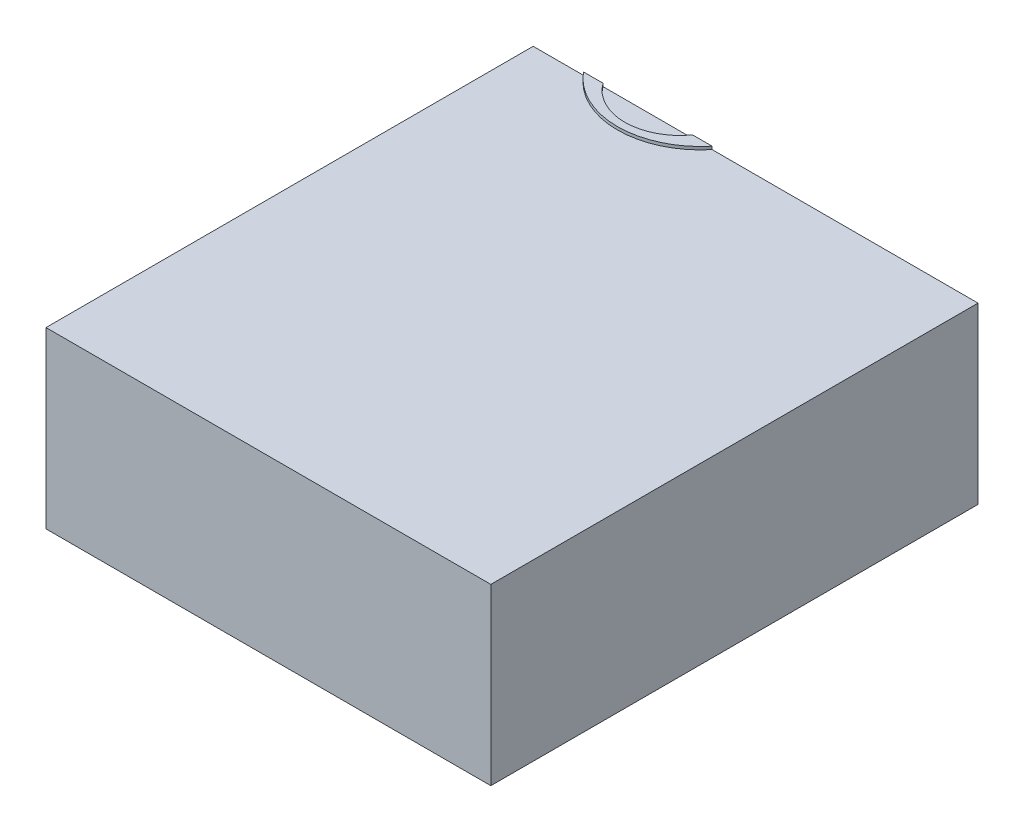
SolidWorks part; units mm, degrees
ref_plane "Front Plane" through (0, 0, 0) normal (0, 0, 1) x (1, 0, 0)
ref_plane "Top Plane" through (0, 0, 0) normal (0, 1, 0) x (1, 0, 0)
ref_plane "Right Plane" through (0, 0, 0) normal (1, 0, 0) x (0, 0, -1)
sketch "Sketch1" plane through (0, 0, 0) normal (0, 1, 0) x (1, 0, 0)
  circle A0 centre (0, 0) radius 28.1
extrude "Boss-Extrude1" add sketch "Sketch1" along normal blind 1
sketch "Sketch2" plane through (0, 1, 0) normal (0, 1, 0) x (1, 0, 0)
  circle A0 centre (0, -7) radius 18.6
extrude "Cut-Extrude1" cut sketch "Sketch2" against normal blind 58.8
sketch "Sketch3" plane through (0, 0, 0) normal (0, -1, 0) x (-1, 0, 0)
  line L1 (111.3415, -182.1414) -> (-111.3415, -182.1414)
  line L2 (111.3415, -182.1414) -> (111.3415, 182.1414)
  line L3 (111.3415, 182.1414) -> (-111.3415, 182.1414)
  line L4 (-111.3415, -182.1414) -> (-111.3415, 182.1414)
  line L5 (111.3415, -182.1414) -> (-111.3415, 182.1414) construction
  line L6 (111.3415, 182.1414) -> (-111.3415, -182.1414) construction
  point P0 (0, 0)
extrude "Boss-Extrude2" add sketch "Sketch3" along normal blind 58.8
sketch "Sketch4" plane through (0, -58.8, 0) normal (0, -1, 0) x (-1, 0, 0)
  line L1 (103.9587, -174.2721) -> (-103.9587, -174.2721)
  line L2 (103.9587, -174.2721) -> (103.9587, 174.2721)
  line L3 (103.9587, 174.2721) -> (-103.9587, 174.2721)
  line L4 (-103.9587, -174.2721) -> (-103.9587, 174.2721)
  line L5 (103.9587, -174.2721) -> (-103.9587, 174.2721) construction
  line L6 (103.9587, 174.2721) -> (-103.9587, -174.2721) construction
  point P0 (0, 0)
extrude "Cut-Extrude2" cut sketch "Sketch4" against normal blind 55.8
sketch "Sketch6" plane through (0, 1, 0) normal (0, 1, 0) x (1, 0, 0)
  circle A1 centre (0, 18.75) radius 3.75
sketch "Sketch9" plane through (0, 0, 0) normal (0, 1, 0) x (1, 0, 0)
  circle A1 centre (0, -7) radius 3
extrude "Cut-Extrude8" cut sketch "Sketch9" against normal blind 10
sketch "Sketch10" plane through (0, 1, 0) normal (0, 1, 0) x (1, 0, 0)
  circle A2 centre (0, 19.85) radius 3.75
extrude "Cut-Extrude9" cut sketch "Sketch10" against normal blind 10
sketch "Sketch11" plane through (0, -58.8, 0) normal (0, -1, 0) x (-1, 0, 0)
  line L0 (38.6585, -17.8586) -> (-111.3415, -17.8586)
  line L25 (111.3415, 182.1414) -> (-111.3415, 182.1414) construction
  line L26 (-111.3415, 182.1414) -> (-111.3415, -182.1414) construction
  line L27 (-111.3415, -17.8586) -> (-111.3415, 182.1414)
  line L28 (-111.3415, 182.1414) -> (111.3415, 182.1414)
  line L29 (111.3415, 182.1414) -> (111.3415, -182.1414)
  line L30 (111.3415, -182.1414) -> (38.6585, -182.1414)
  line L31 (-111.3415, -182.1414) -> (111.3415, -182.1414) construction
  line L32 (38.6585, -182.1414) -> (38.6585, -17.8586)
extrude "Cut-Extrude14" cut sketch "Sketch11" against normal blind 500
extrude "Cut-Extrude5" cut sketch "Sketch6" against normal blind 400
sketch "Sketch8" plane through (0, 0, -182.1414) normal (0, 0, -1) x (-1, 0, 0)
  circle A0 centre (-86.5737, -25.0112) radius 10
extrude "Cut-Extrude7" cut sketch "Sketch8" against normal blind 10 contours A0
